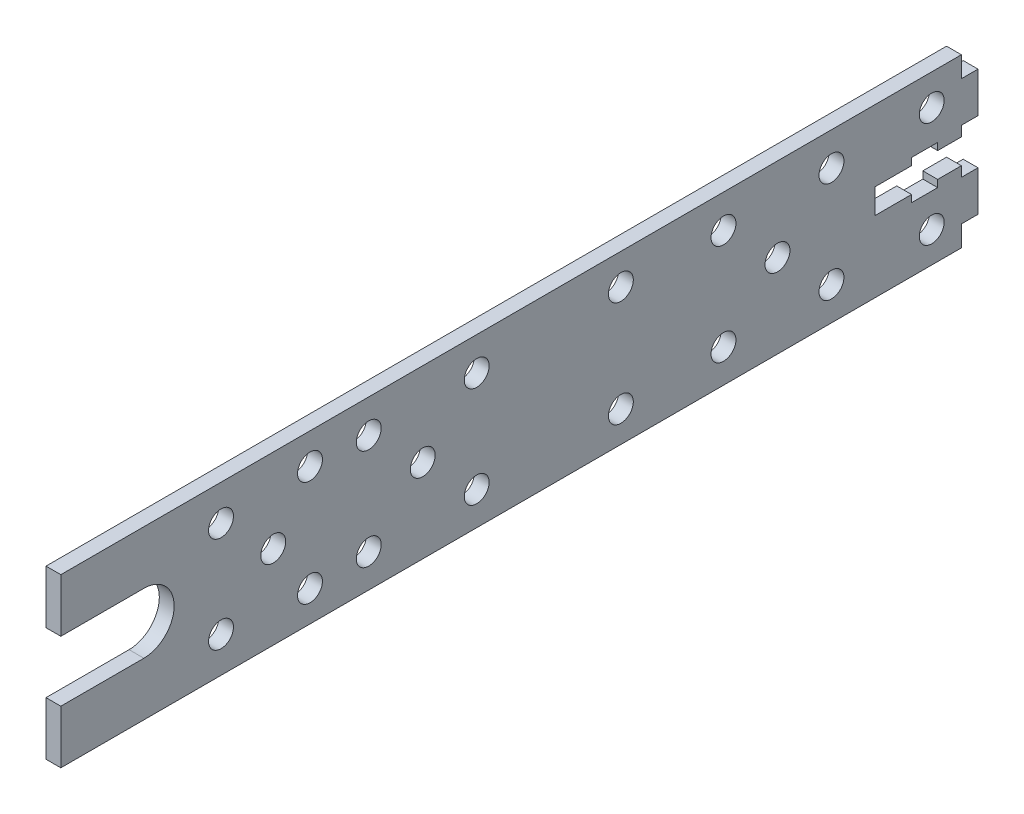
SolidWorks part; units mm, degrees
ref_plane "Front Plane" through (0, 0, 0) normal (0, 0, 1) x (1, 0, 0)
ref_plane "Top Plane" through (0, 0, 0) normal (0, 1, 0) x (1, 0, 0)
ref_plane "Right Plane" through (0, 0, 0) normal (1, 0, 0) x (0, 0, -1)
sketch "Sketch1" plane through (0, 0, 0) normal (1, 0, 0) x (0, 0, -1)
  line L0 (-98.171, 0) -> (98.171, 0) construction
  line L1 (-98.171, 17.907) -> (94.615, 17.907)
  line L2 (-98.171, 17.907) -> (-98.171, 6.477)
  line L3 (-98.171, -17.907) -> (94.615, -17.907)
  line L4 (98.171, 13.462) -> (98.171, 4.826)
  line L5 (94.615, 4.826) -> (94.615, 2.667)
  line L6 (94.615, -2.667) -> (94.615, -4.826)
  line L7 (94.615, 2.667) -> (89.535, 2.667)
  line L8 (94.615, 17.907) -> (94.615, 13.462)
  line L9 (94.615, -2.667) -> (89.535, -2.667)
  line L10 (76.073, 2.667) -> (76.073, -2.667)
  line L11 (86.741, 4.191) -> (86.741, -4.191) construction
  line L12 (-32.258, 10.795) -> (-9.144, 10.795) construction
  line L13 (83.947, 2.667) -> (76.073, 2.667)
  line L14 (89.535, 4.191) -> (83.947, 4.191)
  line L15 (89.535, 4.191) -> (89.535, 2.667)
  line L16 (89.535, -4.191) -> (83.947, -4.191)
  line L17 (83.947, 4.191) -> (83.947, 2.667)
  line L18 (66.802, 10.795) -> (43.688, 10.795) construction
  line L19 (66.802, -10.795) -> (43.688, -10.795) construction
  line L20 (83.947, -2.667) -> (76.073, -2.667)
  line L21 (89.535, -2.667) -> (89.535, -4.191)
  line L22 (83.947, -2.667) -> (83.947, -4.191)
  line L23 (98.171, -4.826) -> (98.171, -13.462)
  line L24 (98.171, 13.462) -> (94.615, 13.462)
  line L25 (98.171, 13.462) -> (98.171, 4.826)
  line L26 (98.171, 4.826) -> (94.615, 4.826)
  line L27 (-32.258, -10.795) -> (-9.144, -10.795) construction
  line L28 (98.171, 13.462) -> (94.615, 4.826) construction
  line L29 (98.171, 4.826) -> (94.615, 13.462) construction
  line L30 (-80.391, 6.477) -> (-98.171, 6.477)
  line L31 (98.171, -4.826) -> (94.615, -4.826)
  line L32 (-20.701, 10.795) -> (-20.701, -10.795) construction
  line L33 (98.171, -13.462) -> (94.615, -4.826) construction
  line L34 (98.171, -4.826) -> (94.615, -13.462) construction
  line L35 (98.171, -13.462) -> (94.615, -13.462)
  line L36 (-80.391, -6.477) -> (-98.171, -6.477)
  line L37 (-98.171, -6.477) -> (-98.171, -17.907)
  line L38 (94.615, -13.462) -> (94.615, -17.907)
  line L39 (55.245, 10.795) -> (55.245, -10.795) construction
  arc A0 (-80.391, -6.477) -> (-80.391, 6.477) centre (-80.391, 0) ccw
  circle A1 centre (-63.881, 10.287) radius 2.667
  circle A2 centre (-63.881, -10.287) radius 2.667
  circle A3 centre (-52.705, 0) radius 2.667
  circle A4 centre (-44.831, 11.303) radius 2.667
  circle A5 centre (21.717, 11.303) radius 2.667
  circle A6 centre (88.265, 11.303) radius 2.667
  circle A7 centre (88.265, -11.303) radius 2.667
  circle A8 centre (21.717, -11.303) radius 2.667
  circle A9 centre (-44.831, -11.303) radius 2.667
  circle A10 centre (-9.144, 10.795) radius 2.667
  circle A11 centre (-32.258, 10.795) radius 2.667
  circle A12 centre (66.802, 10.795) radius 2.667
  circle A13 centre (43.688, 10.795) radius 2.667
  circle A14 centre (43.688, -10.795) radius 2.667
  circle A15 centre (66.802, -10.795) radius 2.667
  circle A16 centre (-32.258, -10.795) radius 2.667
  circle A17 centre (-9.144, -10.795) radius 2.667
  circle A18 centre (-20.701, 0) radius 2.667
  circle A19 centre (55.245, 0) radius 2.667
  point P0 (0, 0)
  point P1 (86.741, 0)
  point P4 (0, 0)
  point P26 (96.393, 9.144)
  point P30 (96.393, -9.144)
  point P44 (76.073, 0)
  dimension "D11" = 12.954
  dimension "D15" = 5.334
  dimension "D26" = 17.78
  dimension "D24" = 39.37
  dimension "D2" = 192.786
  dimension "D3" = 5.334
  dimension "D4" = 18.542
  dimension "D5" = 5.588
  dimension "D6" = 8.636
  dimension "D7" = 8.382
  dimension "D8" = 3.556
  dimension "D9" = 8.636
  dimension "D10" = 9.144
  dimension "D12" = 17.78
  dimension "D13" = 11.43
  dimension "D14" = 11.43
  dimension "D16" = 7.62
  dimension "D17" = 34.29
  dimension "D18" = 150.876
  dimension "D19" = 9.906
  dimension "D20" = 6.604
  dimension "D21" = 76.454
  dimension "D22" = 143.002
  dimension "D23" = 7.112
  dimension "D25" = 115.316
extrude "Boss-Extrude1" add sketch "Sketch1" along normal mid plane 3.175 contours A0 L36 L37 L3 L6 L9 L21 L16 L22 L20 L10 L13 L17 L14 L15 L7 L5 L26 L4 L24 L8 L1 L2 L30 A16 A14 A13 A12 A11 A10 A8 A2 A1 A3 A4 A5
